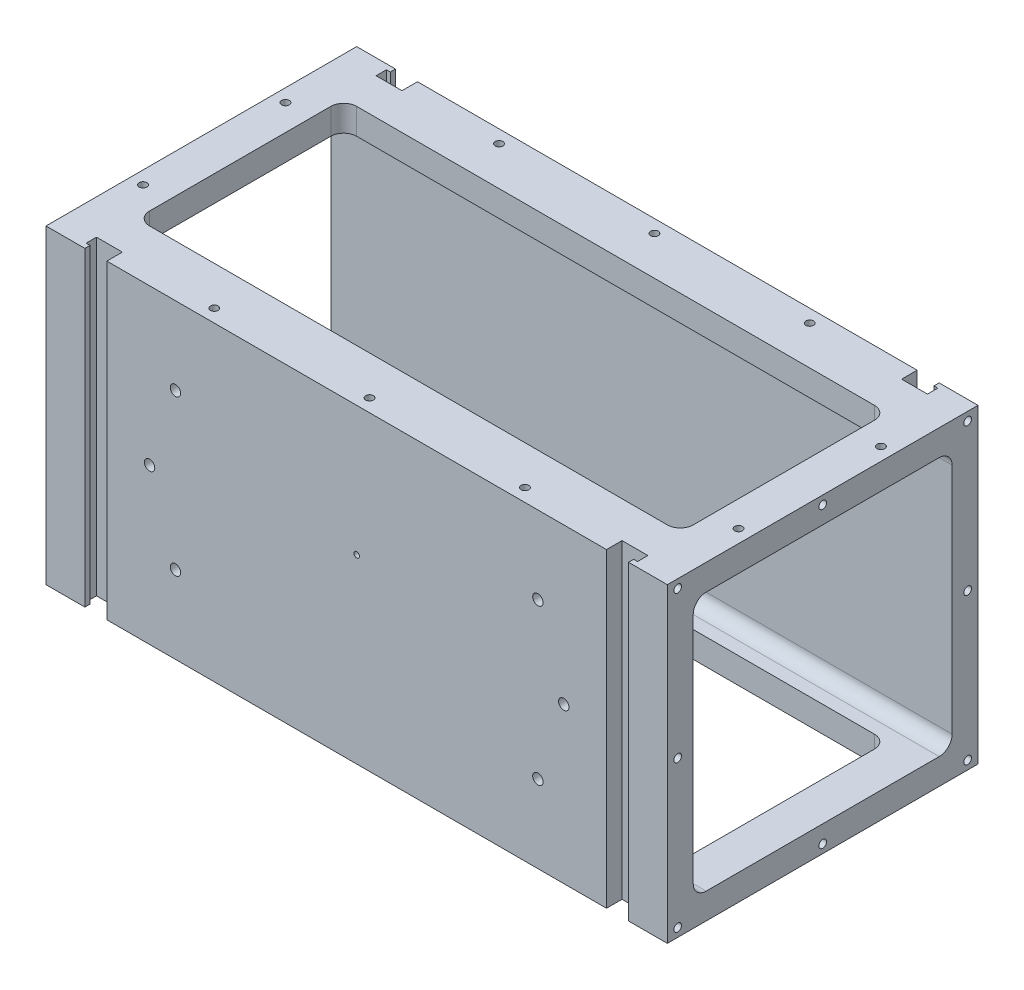
SolidWorks part; units mm, degrees
ref_plane "Front Plane" through (0, 0, 0) normal (0, 0, 1) x (1, 0, 0)
ref_plane "Top Plane" through (0, 0, 0) normal (0, 1, 0) x (1, 0, 0)
ref_plane "Right Plane" through (0, 0, 0) normal (1, 0, 0) x (0, 0, -1)
ref_plane "Plane1" through (0, 0, 76.2) normal (0, 0, 1) x (1, 0, 0)
sketch "Sketch1" plane through (0, 0, 76.2) normal (0, 0, 1) x (1, 0, 0)
  line L0 (-152.4, 76.2) -> (-152.4, -76.2)
  line L1 (-152.4, -76.2) -> (152.4, -76.2)
  line L2 (152.4, -76.2) -> (152.4, 76.2)
  line L3 (152.4, 76.2) -> (-152.4, 76.2)
  dimension "D1" = 304.8
  dimension "D2" = 152.4
  dimension "D3" = 76.2
extrude "Boss-Extrude1" add sketch "Sketch1" against normal blind 152.4
sketch "Sketch2" plane through (0, 76.2, 0) normal (0, 1, 0) x (-1, 0, 0)
  line L0 (133.35, -76.2) -> (133.35, -73.66)
  line L1 (133.35, -73.66) -> (135.255, -73.66)
  line L2 (135.255, -73.66) -> (135.255, -68.58)
  line L3 (135.255, -68.58) -> (122.555, -68.58)
  line L4 (122.555, -68.58) -> (122.555, -76.2)
  line L5 (122.555, -76.2) -> (133.35, -76.2)
  dimension "D1" = 7.62
  dimension "D2" = 10.795
  dimension "D3" = 2.54
  dimension "D4" = 76.2
extrude "Cut-Extrude1" cut sketch "Sketch2" against normal through all
sketch "Sketch6" plane through (-152.4, 0, 0) normal (-1, 0, 0) x (0, 0, 1)
  line L0 (63.5, 63.5) -> (-63.5, 63.5)
  line L1 (-63.5, 63.5) -> (-63.5, -63.5)
  line L2 (-63.5, -63.5) -> (63.5, -63.5)
  line L3 (63.5, -63.5) -> (63.5, 63.5)
  dimension "D1" = 127
  dimension "D2" = 63.5
  dimension "D3" = 127
  dimension "D4" = 63.5
extrude "Cut-Extrude5" cut sketch "Sketch6" against normal through all
sketch "Sketch7" plane through (0, -76.2, 0) normal (0, -1, 0) x (1, 0, 0)
  line L0 (-133.35, -44.45) -> (133.35, -44.45)
  line L1 (133.35, -44.45) -> (133.35, 44.45)
  line L2 (133.35, 44.45) -> (-133.35, 44.45)
  line L3 (-133.35, 44.45) -> (-133.35, -44.45)
extrude "Cut-Extrude6" cut sketch "Sketch7" against normal up to next
sketch "Sketch8" plane through (0, 76.2, 0) normal (0, 1, 0) x (-1, 0, 0)
  line L0 (-133.35, 50.8) -> (-133.35, -50.8)
  line L1 (-133.35, -50.8) -> (133.35, -50.8)
  line L2 (133.35, -50.8) -> (133.35, 50.8)
  line L3 (133.35, 50.8) -> (-133.35, 50.8)
  dimension "D1" = 266.7
  dimension "D2" = 101.6
  dimension "D3" = 50.8
extrude "Cut-Extrude7" cut sketch "Sketch8" against normal through all
hole_wizard "1/4-20 Tapped Hole2" positions "Sketch10" profile "Sketch9" tap size "1/4-20" standard "ANSI Inch"
sketch "Sketch10" plane through (0, 0, -76.2) normal (0, 0, -1) x (-1, 0, 0)
  point P0 (88.9, 38.1)
  point P1 (-88.9, 38.1)
  point P2 (88.9, -38.1)
  point P3 (-88.9, -38.1)
sketch "Sketch9" plane through (-88.9, 38.1, -76.2) normal (1, 0, 0) x (0, 1, 0)
  line L0 (0, 0) -> (0, 10.4238)
  line L1 (0, 10.4238) -> (2.5527, 8.89)
  line L2 (2.5527, 8.89) -> (2.5527, 0)
  line L5 (2.5527, 0) -> (0, 0)
  line L10 (0, 10.4238) -> (-2.5527, 8.89) construction
  line L11 (0, -6.35) -> (0, 107.95) construction
  dimension "Tap Drill Dia." = 5.1054
  dimension "Tap Drill Depth" = 8.89
  dimension "Drill Angle" = 118
hole_wizard "#6-32 Tapped Hole1" positions "Sketch12" profile "Sketch11" tap size "#6-32" standard "ANSI Inch"
sketch "Sketch12" plane through (0, 0, -76.2) normal (0, 0, -1) x (-1, 0, 0)
  point P0 (0, 12.7)
sketch "Sketch11" plane through (0, 12.7, -76.2) normal (1, 0, 0) x (0, 1, 0)
  line L0 (0, 0) -> (0, 10.2005)
  line L1 (0, 10.2005) -> (1.3525, 9.3878)
  line L2 (1.3525, 9.3878) -> (1.3525, 0)
  line L5 (1.3525, 0) -> (0, 0)
  line L10 (0, 10.2005) -> (-1.3526, 9.3878) construction
  line L11 (0, -6.35) -> (0, 107.95) construction
  dimension "Tap Drill Dia." = 2.7051
  dimension "Tap Drill Depth" = 9.3878
  dimension "Drill Angle" = 118
hole_wizard "1/4-20 Tapped Hole1" positions "Sketch14" profile "Sketch13" tap size "1/4-20" standard "ANSI Inch"
sketch "Sketch14" plane through (0, 0, 76.2) normal (0, 0, 1) x (1, 0, 0)
  point P0 (-88.9, -38.1)
  point P1 (88.9, -38.1)
  point P2 (88.9, 38.1)
  point P3 (-88.9, 38.1)
sketch "Sketch13" plane through (-88.9, -38.1, 76.2) normal (1, 0, 0) x (0, -1, 0)
  line L0 (0, 0) -> (0, 10.4238)
  line L1 (0, 10.4238) -> (2.5527, 8.89)
  line L2 (2.5527, 8.89) -> (2.5527, 0)
  line L5 (2.5527, 0) -> (0, 0)
  line L10 (0, 10.4238) -> (-2.5527, 8.89) construction
  line L11 (0, -6.35) -> (0, 107.95) construction
  dimension "Tap Drill Dia." = 5.1054
  dimension "Tap Drill Depth" = 8.89
  dimension "Drill Angle" = 118
hole_wizard "#10-24 Tapped Hole1" positions "Sketch16" profile "Sketch15" tap size "#10-24" standard "ANSI Inch"
sketch "Sketch16" plane through (0, 76.2, 0) normal (0, 1, 0) x (1, 0, 0)
  line L0 (152.4, 76.2) -> (-122.555, 76.2) construction
  line L1 (-55, -76.2) -> (55, -76.2) construction
  line L2 (-152.4, 76.2) -> (-152.4, -76.2) construction
  line L3 (152.4, 76.2) -> (152.4, -76.2) construction
  point P0 (-146.05, -34.925)
  point P1 (-76.2, -69.85)
  point P2 (146.05, -34.925)
  point P3 (76.2, -69.85)
  point P4 (146.05, 34.925)
  point P5 (76.2, 69.85)
  point P6 (-146.05, 34.925)
  point P7 (-76.2, 69.85)
  dimension "D1" = 6.35
  dimension "D2" = 6.35
  dimension "D3" = 6.35
  dimension "D4" = 6.35
  dimension "D5" = 76.2
  dimension "D6" = 76.2
  dimension "D7" = 76.2
  dimension "D8" = 76.2
sketch "Sketch15" plane through (-146.05, 76.2, 34.925) normal (1, 0, 0) x (0, 0, 1)
  line L0 (0, 0) -> (0, 8.8904)
  line L1 (0, 8.8904) -> (1.8986, 7.7495)
  line L2 (1.8986, 7.7495) -> (1.8986, 0)
  line L5 (1.8986, 0) -> (0, 0)
  line L10 (0, 8.8904) -> (-1.8987, 7.7495) construction
  line L11 (0, -6.35) -> (0, 107.95) construction
  dimension "Tap Drill Dia." = 3.7973
  dimension "Tap Drill Depth" = 7.7495
  dimension "Drill Angle" = 118
hole_wizard "#10-24 Tapped Hole2" positions "Sketch18" profile "Sketch17" tap size "#10-24" standard "ANSI Inch"
sketch "Sketch18" plane through (0, 76.2, 0) normal (0, 1, 0) x (1, 0, 0)
  line L0 (152.4, 76.2) -> (-122.555, 76.2) construction
  line L1 (-55, -76.2) -> (55, -76.2) construction
  point P0 (0, -69.85)
  point P1 (0, 69.85)
  dimension "D1" = 6.35
  dimension "D2" = 6.35
sketch "Sketch17" plane through (0, 76.2, 69.85) normal (1, 0, 0) x (0, 0, 1)
  line L0 (0, 0) -> (0, 13.9704)
  line L1 (0, 13.9704) -> (1.8986, 12.8295)
  line L2 (1.8986, 12.8295) -> (1.8986, 0)
  line L5 (1.8986, 0) -> (0, 0)
  line L10 (0, 13.9704) -> (-1.8986, 12.8295) construction
  line L11 (0, -6.35) -> (0, 107.95) construction
  dimension "Tap Drill Dia." = 3.7973
  dimension "Tap Drill Depth" = 12.8295
  dimension "Drill Angle" = 118
hole_wizard "#10-24 Tapped Hole6" positions "Sketch24" profile "Sketch23" tap size "#10-24" standard "ANSI Inch"
sketch "Sketch24" plane through (-152.4, 0, 0) normal (-1, 0, 0) x (0, 0, 1)
  line L0 (-76.2, 76.2) -> (76.2, 76.2) construction
  line L1 (-76.2, -76.2) -> (76.2, -76.2) construction
  line L2 (-76.2, 76.2) -> (-76.2, -76.2) construction
  line L3 (76.2, 76.2) -> (76.2, -76.2) construction
  point P0 (-25.4, -72.009)
  point P1 (25.4, -72.009)
  point P2 (72.009, 0)
  point P3 (25.4, 72.009)
  point P4 (-72.009, 0)
  point P5 (-25.4, 72.009)
  dimension "D1" = 4.191
  dimension "D2" = 4.191
  dimension "D3" = 4.191
  dimension "D4" = 4.191
  dimension "D5" = 4.191
  dimension "D6" = 4.191
  dimension "D7" = 50.8
sketch "Sketch23" plane through (-152.4, -72.009, -25.4) normal (0, 1, 0) x (0, 0, 1)
  line L0 (0, 0) -> (0, 11.4304)
  line L1 (0, 11.4304) -> (1.8986, 10.2895)
  line L2 (1.8986, 10.2895) -> (1.8986, 0)
  line L5 (1.8986, 0) -> (0, 0)
  line L10 (0, 11.4304) -> (-1.8987, 10.2895) construction
  line L11 (0, -6.35) -> (0, 107.95) construction
  dimension "Tap Drill Dia." = 3.7973
  dimension "Tap Drill Depth" = 10.2895
  dimension "Drill Angle" = 118
hole_wizard "#10-24 Tapped Hole5" positions "Sketch26" profile "Sketch25" tap size "#10-24" standard "ANSI Inch"
sketch "Sketch26" plane through (152.4, 0, 0) normal (1, 0, 0) x (0, 0, -1)
  line L0 (76.2, -76.2) -> (-76.2, -76.2) construction
  line L1 (76.2, 76.2) -> (-76.2, 76.2) construction
  line L2 (-76.2, -76.2) -> (-76.2, 76.2) construction
  line L3 (76.2, 76.2) -> (76.2, -76.2) construction
  line L4 (76.2, -76.2) -> (76.2, 76.2) construction
  line L6 (-76.2, 76.2) -> (-76.2, -76.2) construction
  point P0 (71.12, 72.009)
  point P1 (71.12, -72.009)
  point P3 (-71.12, -72.009)
  point P4 (0, -72.009)
  point P5 (-71.12, 72.009)
  point P6 (-71.12, 0)
  point P7 (0.0334, 72.009)
  point P20 (71.12, 0)
  point P25 (76.2, 0)
  dimension "D2" = 5.08
  dimension "D3" = 5.08
  dimension "D4" = 4.191
  dimension "D5" = 5.08
  dimension "D6" = 5.08
  dimension "D7" = 4.191
  dimension "D8" = 4.191
  dimension "D9" = 4.191
  dimension "D11" = 4.191
  dimension "D12" = 4.191
  dimension "D13" = 5.08
  dimension "D14" = 5.08
sketch "Sketch25" plane through (152.4, 72.009, -71.12) normal (0, 1, 0) x (0, 0, -1)
  line L0 (0, 0) -> (0, 11.4304)
  line L1 (0, 11.4304) -> (1.8986, 10.2895)
  line L2 (1.8986, 10.2895) -> (1.8986, 0)
  line L5 (1.8986, 0) -> (0, 0)
  line L10 (0, 11.4304) -> (-1.8987, 10.2895) construction
  line L11 (0, -6.35) -> (0, 107.95) construction
  dimension "Tap Drill Dia." = 3.7973
  dimension "Tap Drill Depth" = 10.2895
  dimension "Drill Angle" = 118
hole_wizard "#6-32 Tapped Hole2" positions "Sketch28" profile "Sketch27" tap size "#6-32" standard "ANSI Inch"
sketch "Sketch28" plane through (0, 0, 76.2) normal (0, 0, 1) x (1, 0, 0)
  point P0 (0, 12.7)
sketch "Sketch27" plane through (0, 12.7, 76.2) normal (1, 0, 0) x (0, -1, 0)
  line L0 (0, 0) -> (0, 10.2005)
  line L1 (0, 10.2005) -> (1.3525, 9.3878)
  line L2 (1.3525, 9.3878) -> (1.3525, 0)
  line L5 (1.3525, 0) -> (0, 0)
  line L10 (0, 10.2005) -> (-1.3526, 9.3878) construction
  line L11 (0, -6.35) -> (0, 107.95) construction
  dimension "Tap Drill Dia." = 2.7051
  dimension "Tap Drill Depth" = 9.3878
  dimension "Drill Angle" = 118
fillet "Fillet1" radius 6.35 4 edges at (-133.35, 69.85, 50.8) (133.35, 69.85, -50.8) (-133.35, 69.85, -50.8) (133.35, 69.85, 50.8)
fillet "Fillet2" radius 6.35 4 edges at (0, 63.5, 63.5) (0, -63.5, 63.5) (0, 63.5, -63.5) (0, -63.5, -63.5)
mirror "Mirror1" about plane through (0, 0, 0) normal (1, 0, 0) of "Cut-Extrude1"
mirror "Mirror2" about plane through (0, 0, 0) normal (0, 0, 1) of "Mirror1", "Cut-Extrude1"
mirror "Mirror3" about plane through (0, 0, 0) normal (0, 1, 0) of "#10-24 Tapped Hole2", "#10-24 Tapped Hole1"
mirror "Mirror4" about plane through (0, 0, 0) normal (1, 0, 0) of "#10-24 Tapped Hole5"
hole_wizard "1/4-20 Tapped Hole3" positions "Sketch30" profile "Sketch29" tap size "1/4-20" standard "ANSI Inch"
sketch "Sketch30" plane through (0, 0, 76.2) normal (0, 0, 1) x (1, 0, 0)
  line L0 (-152.4, 76.2) -> (-152.4, -76.2) construction
  line L1 (152.4, -76.2) -> (152.4, 76.2) construction
  line L2 (-122.555, -76.2) -> (122.555, -76.2) construction
  point P0 (-101.6, 0)
  point P2 (101.6, 0)
  point P7 (152.4, 0)
  dimension "D1" = 203.2
  dimension "D2" = 50.8
  dimension "D3" = 50.8
  dimension "D4" = 76.2
cosmetic thread "Hole Thread1" parameters "D2"=6.35
cosmetic thread "Hole Thread2" parameters "D2"=6.35
sketch "Sketch29" plane through (-101.6, 0, 76.2) normal (1, 0, 0) x (0, -1, 0)
  line L0 (0, 0) -> (0, 9.3443)
  line L1 (0, 9.3443) -> (2.5527, 7.8105)
  line L2 (2.5527, 7.8105) -> (2.5527, 0)
  line L5 (2.5527, 0) -> (0, 0)
  line L10 (0, 9.3443) -> (-2.5527, 7.8105) construction
  line L11 (0, -6.35) -> (0, 107.95) construction
  dimension "Tap Drill Dia." = 5.1054
  dimension "Tap Drill Depth" = 7.8105
  dimension "Drill Angle" = 118
equation "\"D4@Sketch26\"=\"D12@Sketch26\""
equation "\"D2@Sketch6\"=\"D1@Sketch6\"/2"
equation "\"D4@Sketch6\"=\"D3@Sketch6\"/2"
equation "\"D3@Sketch1\"=\"D2@Sketch1\"/2"
equation "\"D2@Sketch16\"=\"D1@Sketch16\""
equation "\"D3@Sketch16\"=\"D2@Sketch16\""
equation "\"D4@Sketch16\"=\"D1@Sketch16\""
equation "\"D6@Sketch16\"=\"D5@Sketch16\""
equation "\"D7@Sketch16\"=\"D5@Sketch16\""
equation "\"D8@Sketch16\"=\"D7@Sketch16\""
equation "\"D2@Sketch18\"=\"D1@Sketch18\""
equation "\"D8@Sketch26\"=\"D7@Sketch26\""
equation "\"D9@Sketch26\"=\"D7@Sketch26\""
equation "\"D3@Sketch8\"=\"D2@Sketch8\"/2"
equation "\"D2@Sketch24\"=\"D1@Sketch24\""
equation "\"D6@Sketch24\"=\"D2@Sketch24\""
equation "\"D3@Sketch24\"=\"D1@Sketch24\""
equation "\"D5@Sketch24\"=\"D1@Sketch24\""
equation "\"D4@Sketch24\"=\"D5@Sketch24\""
equation "\"D7@Sketch26\"=\"D12@Sketch26\""
equation "\"D11@Sketch26\"=\"D12@Sketch26\""
equation "\"D2@Sketch26\"=\"D3@Sketch26\""
equation "\"D5@Sketch26\"=\"D2@Sketch26\""
equation "\"D6@Sketch26\"=\"D3@Sketch26\""
equation "\"D13@Sketch26\"=\"D6@Sketch26\""
equation "\"D14@Sketch26\"=\"D6@Sketch26\""
